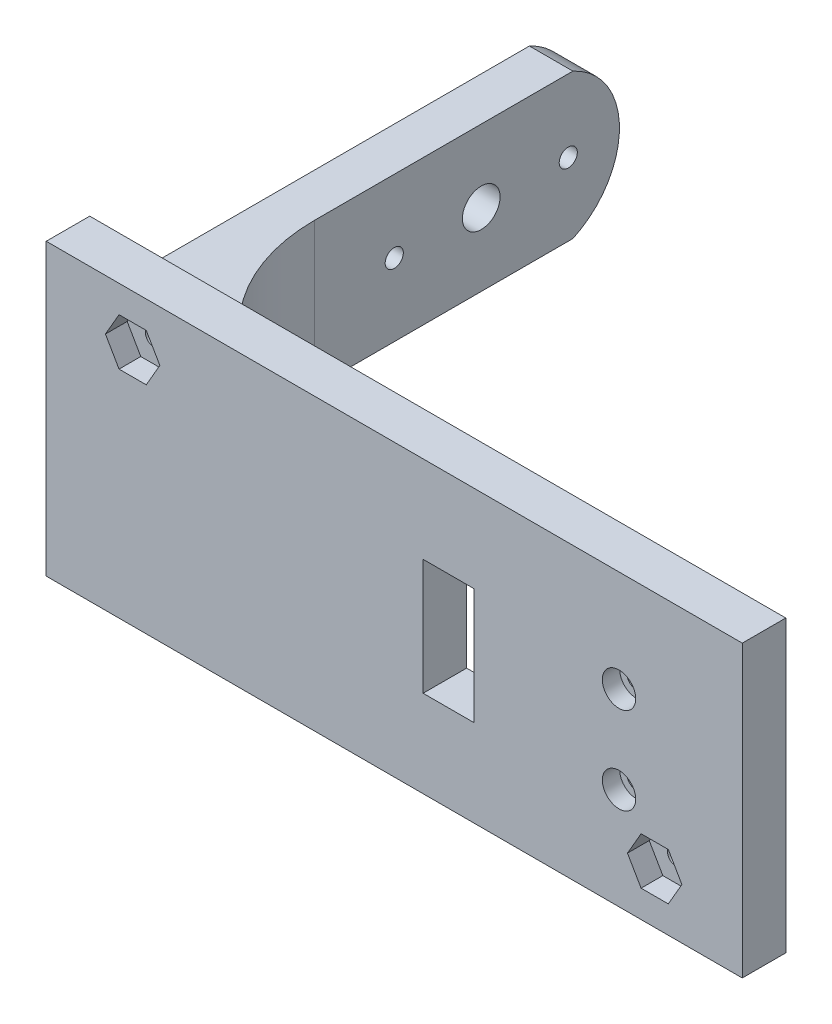
SolidWorks part; units mm, degrees
ref_plane "Front Plane" through (0, 0, 0) normal (0, 0, 1) x (1, 0, 0)
ref_plane "Top Plane" through (0, 0, 0) normal (0, 1, 0) x (1, 0, 0)
ref_plane "Right Plane" through (0, 0, 0) normal (1, 0, 0) x (0, 0, -1)
sketch "Sketch1" plane through (0, 0, 0) normal (0, 1, 0) x (1, 0, 0)
  line L0 (0, 0) -> (0, -59.69)
  line L1 (31.75, -91.44) -> (69.85, -91.44)
  line L2 (101.6, -59.69) -> (101.6, 0)
  line L3 (101.6, 0) -> (114.3, 0)
  line L4 (114.3, 0) -> (114.3, -99.06)
  line L5 (114.3, -99.06) -> (-7.62, -99.06)
  line L6 (-7.62, -99.06) -> (-7.62, 0)
  line L7 (-7.62, 0) -> (0, 0)
  arc A0 (69.85, -91.44) -> (101.6, -59.69) centre (69.85, -59.69) ccw
  arc A1 (0, -59.69) -> (31.75, -91.44) centre (31.75, -59.69) ccw
  point P11 (101.6, -91.44)
  point P14 (0, -91.44)
  dimension "D6" = 31.75
  dimension "D1" = 101.6
  dimension "D2" = 7.62
  dimension "D3" = 12.7
  dimension "D4" = 7.62
  dimension "D5" = 91.44
extrude "Boss-Extrude1" add sketch "Sketch1" along normal blind 25.4
sketch "Sketch2" plane through (0, 0, 0) normal (1, 0, 0) x (0, 0, -1)
  line L0 (0, 25.4) -> (0, 0) construction
  line L2 (0, 25.4) -> (0, 0) construction
  circle A2 centre (-15.24, 12.7) radius 1.5875
  circle A3 centre (-45.72, 12.7) radius 1.5875
  circle A4 centre (-30.48, 12.7) radius 3.302
  point P4 (0, 12.7)
  dimension "D1" = 30.48
  dimension "D3" = 3.175
  dimension "D4" = 6.604
  dimension "D8" = 3.175
  dimension "D2" = 15.24
  dimension "D5" = 15.24
sketch "Sketch4" plane through (101.6, 0, 0) normal (-1, 0, 0) x (0, 0, 1)
  line L0 (0, 25.4) -> (0, 0) construction
  circle A0 centre (30.48, 12.7) radius 3.302
  point P4 (0, 12.7)
  dimension "D1" = 30.48
  dimension "D2" = 6.604
extrude "Cut-Extrude2" cut sketch "Sketch4" against normal blind 7.62 contours A0
extrude "Cut-Extrude3" cut sketch "Sketch2" against normal blind 7.62
sketch "Sketch6" plane through (0, 0, 99.06) normal (0, 0, 1) x (1, 0, 0)
  line L0 (-7.62, 25.4) -> (114.3, 25.4) construction
  line L1 (-7.62, 25.4) -> (114.3, 25.4)
  line L2 (-7.62, 25.4) -> (-7.62, 38.1)
  line L3 (-7.62, 38.1) -> (114.3, 38.1)
  line L4 (114.3, 25.4) -> (114.3, 38.1)
  line L5 (-7.62, 0) -> (114.3, 0) construction
  line L6 (-7.62, 0) -> (114.3, 0)
  line L7 (-7.62, 0) -> (-7.62, -12.7)
  line L8 (-7.62, -12.7) -> (114.3, -12.7)
  line L9 (114.3, 0) -> (114.3, -12.7)
  line L10 (-7.62, 25.4) -> (-7.62, 0) construction
  line L11 (114.3, 25.4) -> (114.3, 0) construction
  point P13 (53.34, 25.4)
  point P14 (53.34, 0)
  dimension "D1" = 50.8
extrude "Boss-Extrude2" add sketch "Sketch6" against normal up to surface (7.62 mm away) up to face at (50.8, 12.7, 91.44)
sketch "Sketch7" plane through (0, 0, 99.06) normal (0, 0, 1) x (1, 0, 0)
  line L0 (-7.62, 38.1) -> (-7.62, -12.7) construction
  line L1 (12.2844, 29.21) -> (9.9014, 33.3375)
  line L2 (9.9014, 33.3375) -> (5.1354, 33.3375)
  line L3 (5.1354, 33.3375) -> (2.7524, 29.21)
  line L4 (2.7524, 29.21) -> (5.1354, 25.0825)
  line L5 (5.1354, 25.0825) -> (9.9014, 25.0825)
  line L6 (9.9014, 25.0825) -> (12.2844, 29.21)
  line L7 (103.7244, -3.81) -> (101.3414, 0.3175)
  line L8 (101.3414, 0.3175) -> (96.5754, 0.3175)
  line L9 (96.5754, 0.3175) -> (94.1924, -3.81)
  line L10 (94.1924, -3.81) -> (96.5754, -7.9375)
  line L11 (96.5754, -7.9375) -> (101.3414, -7.9375)
  line L12 (101.3414, -7.9375) -> (103.7244, -3.81)
  line L13 (114.3, 25.4) -> (114.3, 38.1) construction
  circle A2 centre (7.5184, 29.21) radius 4.1275 construction
  circle A3 centre (98.9584, -3.81) radius 4.1275 construction
  point P21 (-7.62, 12.7)
  dimension "D1" = 8.255
  dimension "D2" = 8.255
  dimension "D3" = 16.51
  dimension "D4" = 33.02
  dimension "D5" = 91.44
  dimension "D6" = 15.3416
extrude "Cut-Extrude4" cut sketch "Sketch7" against normal blind 3.81
sketch "Sketch8" plane through (0, 0, 99.06) normal (0, 0, 1) x (1, 0, 0)
  circle A0 centre (7.5184, 29.21) radius 4.1275
  circle A1 centre (98.9584, -3.81) radius 4.1275
  dimension "D1" = 8.255
  dimension "D2" = 8.255
sketch "Sketch10" plane through (-7.62, 0, 0) normal (-1, 0, 0) x (0, 0, 1)
  circle A1 centre (15.24, 12.7) radius 2.921
  circle A2 centre (45.72, 12.7) radius 2.921
  dimension "D1" = 5.842
  dimension "D2" = 5.842
extrude "Cut-Extrude5" cut sketch "Sketch10" against normal blind 3.048
sketch "Sketch11" plane through (0, 0, 95.25) normal (0, 0, 1) x (1, 0, 0)
  circle A0 centre (7.5184, 29.21) radius 1.5875
  circle A1 centre (98.9584, -3.81) radius 1.5875
  dimension "D1" = 3.175
  dimension "D2" = 3.175
extrude "Cut-Extrude6" cut sketch "Sketch11" against normal through all
sketch "Sketch12" plane through (0, 0, 99.06) normal (0, 0, 1) x (1, 0, 0)
  line L0 (-7.62, -12.7) -> (114.3, -12.7) construction
  line L1 (67.2846, 22.86) -> (58.3946, 22.86)
  line L2 (67.2846, 22.86) -> (67.2846, 2.54)
  line L3 (67.2846, 2.54) -> (58.3946, 2.54)
  line L4 (58.3946, 22.86) -> (58.3946, 2.54)
  line L6 (-7.62, 25.4) -> (-7.62, 38.1) construction
  dimension "D1" = 15.24
  dimension "D2" = 66.0146
  dimension "D3" = 8.89
  dimension "D4" = 20.32
extrude "Cut-Extrude7" cut sketch "Sketch12" against normal up to next
sketch "Sketch14" plane through (-7.62, 0, 0) normal (-1, 0, 0) x (0, 0, 1)
  line L0 (0, 25.4) -> (91.44, 25.4) construction
  line L1 (0, 0) -> (91.44, 0) construction
  line L2 (14.4264, 25.4) -> (0, 25.4)
  line L3 (0, 25.4) -> (0, 0)
  line L4 (0, 0) -> (14.4264, 0)
  arc A0 (14.4264, 25.4) -> (14.4264, 0) centre (20.2462, 12.7) ccw
  dimension "D1" = 13.97
extrude "Cut-Extrude8" cut sketch "Sketch14" against normal through all both and the other way through all
sketch "Sketch15" plane through (0, 0, 91.44) normal (0, 0, -1) x (-1, 0, 0)
  line L0 (-67.2846, 22.86) -> (-67.2846, 2.54) construction
  line L1 (-114.3, 38.1) -> (-114.3, 25.4) construction
  circle A0 centre (-92.71, 20.32) radius 1.651
  circle A1 centre (-92.71, 5.08) radius 1.651
  point P6 (-67.2846, 12.7)
  dimension "D1" = 3.302
  dimension "D2" = 3.302
  dimension "D3" = 15.24
  dimension "D4" = 7.62
  dimension "D5" = 21.59
extrude "Cut-Extrude9" cut sketch "Sketch15" against normal through all
sketch "Sketch16" plane through (0, 0, 99.06) normal (0, 0, 1) x (1, 0, 0)
  circle A0 centre (92.71, 20.32) radius 2.921
  circle A1 centre (92.71, 5.08) radius 2.921
  dimension "D1" = 5.842
  dimension "D2" = 5.842
extrude "Cut-Extrude10" cut sketch "Sketch16" against normal blind 3.048
sketch "Sketch17" plane through (0, 38.1, 0) normal (0, 1, 0) x (1, 0, 0)
  line L1 (114.3, -91.44) -> (67.9768, -91.44)
  line L2 (114.3, -91.44) -> (114.3, -3.3811)
  line L3 (114.3, -3.3811) -> (67.9768, -3.3811)
  line L4 (67.9768, -91.44) -> (67.9768, -3.3811)
extrude "Cut-Extrude11" cut sketch "Sketch17" against normal through all
